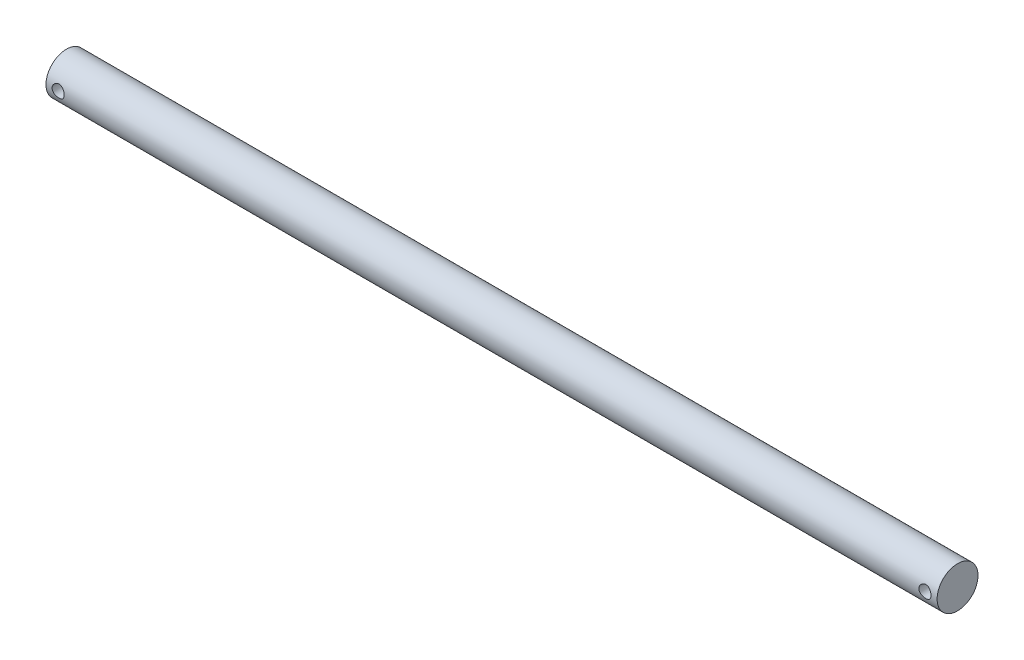
SolidWorks part; units mm, degrees
material "Aleación 1060"
ref_plane "Alzado" through (0, 0, 0) normal (0, 0, 1) x (1, 0, 0)
ref_plane "Planta" through (0, 0, 0) normal (0, 1, 0) x (1, 0, 0)
ref_plane "Vista lateral" through (0, 0, 0) normal (1, 0, 0) x (0, 0, -1)
sketch "Croquis1" plane through (0, 0, 0) normal (1, 0, 0) x (0, 0, -1)
  circle A0 centre (0, 0) radius 5.05
  dimension "D1" = 10.1
extrude "Saliente-Extruir1" add sketch "Croquis1" along normal blind 220
sketch "Croquis2" plane through (0, 0, 0) normal (0, 0, 1) x (1, 0, 0)
  line L0 (0, 0) -> (220, 0) construction
  line L1 (220, -5.05) -> (220, 5.05) construction
  line L2 (0, 5.05) -> (0, -5.05) construction
  circle A0 centre (3, 0) radius 1.5
  circle A1 centre (217, 0) radius 1.5
  dimension "D1" = 3
  dimension "D2" = 3
  dimension "D3" = 3
  dimension "D4" = 3
extrude "Cortar-Extruir1" cut sketch "Croquis2" against normal up to next and the other way up to next
